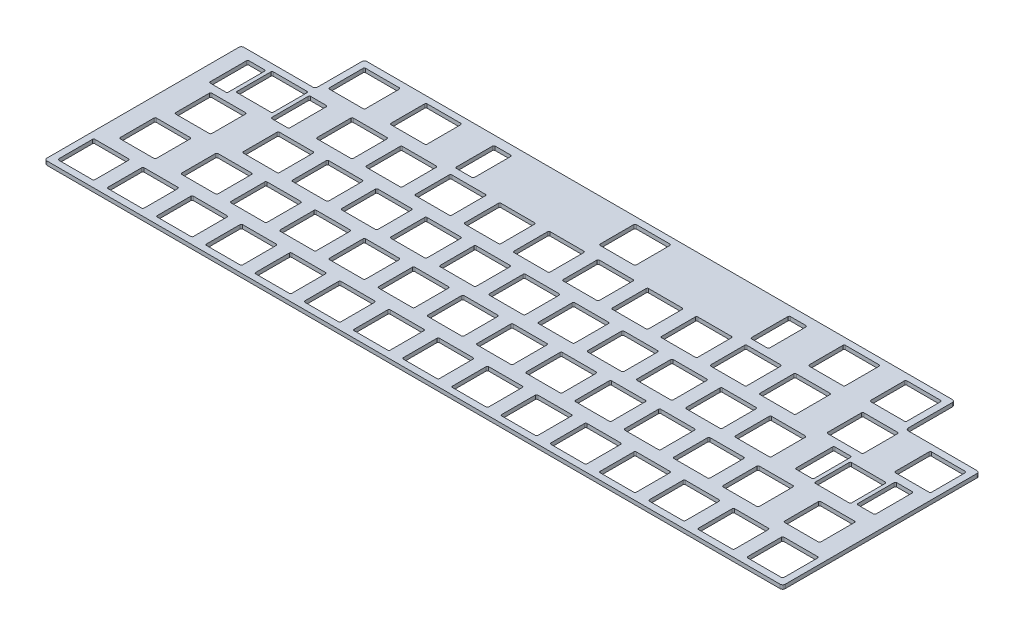
SolidWorks part; units mm, degrees
ref_plane "Front Plane" through (0, 0, 0) normal (0, 0, 1) x (1, 0, 0)
ref_plane "Top Plane" through (0, 0, 0) normal (0, 1, 0) x (1, 0, 0)
ref_plane "Right Plane" through (0, 0, 0) normal (1, 0, 0) x (0, 0, -1)
sketch "Sketch2" plane through (0, 0, 0) normal (0, -1, 0) x (1, 0, 0)
  line L0 (3.025, -2.525) -> (16.025, -2.525)
  line L1 (3.025, -16.525) -> (16.025, -16.525)
  line L2 (2.525, -3.025) -> (2.525, -16.025)
  line L3 (16.525, -3.025) -> (16.525, -16.025)
  line L4 (22.075, -2.525) -> (35.075, -2.525)
  line L5 (22.075, -16.525) -> (35.075, -16.525)
  line L6 (21.575, -3.025) -> (21.575, -16.025)
  line L7 (35.575, -3.025) -> (35.575, -16.025)
  line L8 (41.125, -2.525) -> (54.125, -2.525)
  line L9 (41.125, -16.525) -> (54.125, -16.525)
  line L10 (40.625, -3.025) -> (40.625, -16.025)
  line L11 (54.625, -3.025) -> (54.625, -16.025)
  line L12 (60.175, -2.525) -> (73.175, -2.525)
  line L13 (60.175, -16.525) -> (73.175, -16.525)
  line L14 (59.675, -3.025) -> (59.675, -16.025)
  line L15 (73.675, -3.025) -> (73.675, -16.025)
  line L16 (79.225, -2.525) -> (92.225, -2.525)
  line L17 (79.225, -16.525) -> (92.225, -16.525)
  line L18 (78.725, -3.025) -> (78.725, -16.025)
  line L19 (92.725, -3.025) -> (92.725, -16.025)
  line L20 (98.275, -2.525) -> (111.275, -2.525)
  line L21 (98.275, -16.525) -> (111.275, -16.525)
  line L22 (97.775, -3.025) -> (97.775, -16.025)
  line L23 (111.775, -3.025) -> (111.775, -16.025)
  line L24 (117.325, -2.525) -> (130.325, -2.525)
  line L25 (117.325, -16.525) -> (130.325, -16.525)
  line L26 (116.825, -3.025) -> (116.825, -16.025)
  line L27 (130.825, -3.025) -> (130.825, -16.025)
  line L28 (136.375, -2.525) -> (149.375, -2.525)
  line L29 (136.375, -16.525) -> (149.375, -16.525)
  line L30 (135.875, -3.025) -> (135.875, -16.025)
  line L31 (149.875, -3.025) -> (149.875, -16.025)
  line L32 (155.425, -2.525) -> (168.425, -2.525)
  line L33 (155.425, -16.525) -> (168.425, -16.525)
  line L34 (154.925, -3.025) -> (154.925, -16.025)
  line L35 (168.925, -3.025) -> (168.925, -16.025)
  line L36 (174.475, -2.525) -> (187.475, -2.525)
  line L37 (174.475, -16.525) -> (187.475, -16.525)
  line L38 (173.975, -3.025) -> (173.975, -16.025)
  line L39 (187.975, -3.025) -> (187.975, -16.025)
  line L40 (193.525, -2.525) -> (206.525, -2.525)
  line L41 (193.525, -16.525) -> (206.525, -16.525)
  line L42 (193.025, -3.025) -> (193.025, -16.025)
  line L43 (207.025, -3.025) -> (207.025, -16.025)
  line L44 (212.575, -2.525) -> (225.575, -2.525)
  line L45 (212.575, -16.525) -> (225.575, -16.525)
  line L46 (212.075, -3.025) -> (212.075, -16.025)
  line L47 (226.075, -3.025) -> (226.075, -16.025)
  line L48 (231.625, -2.525) -> (244.625, -2.525)
  line L49 (231.625, -16.525) -> (244.625, -16.525)
  line L50 (231.125, -3.025) -> (231.125, -16.025)
  line L51 (245.125, -3.025) -> (245.125, -16.025)
  line L52 (250.675, -2.525) -> (263.675, -2.525)
  line L53 (250.675, -16.525) -> (263.675, -16.525)
  line L54 (250.175, -3.025) -> (250.175, -16.025)
  line L55 (264.175, -3.025) -> (264.175, -16.025)
  line L56 (269.725, -2.525) -> (282.725, -2.525)
  line L57 (269.725, -16.525) -> (282.725, -16.525)
  line L58 (269.225, -3.025) -> (269.225, -16.025)
  line L59 (283.225, -3.025) -> (283.225, -16.025)
  line L60 (7.7875, -21.575) -> (20.7875, -21.575)
  line L61 (7.7875, -35.575) -> (20.7875, -35.575)
  line L62 (7.2875, -22.075) -> (7.2875, -35.075)
  line L63 (21.2875, -22.075) -> (21.2875, -35.075)
  line L64 (31.6, -21.575) -> (44.6, -21.575)
  line L65 (31.6, -35.575) -> (44.6, -35.575)
  line L66 (31.1, -22.075) -> (31.1, -35.075)
  line L67 (45.1, -22.075) -> (45.1, -35.075)
  line L68 (50.65, -21.575) -> (63.65, -21.575)
  line L69 (50.65, -35.575) -> (63.65, -35.575)
  line L70 (50.15, -22.075) -> (50.15, -35.075)
  line L71 (64.15, -22.075) -> (64.15, -35.075)
  line L72 (69.7, -21.575) -> (82.7, -21.575)
  line L73 (69.7, -35.575) -> (82.7, -35.575)
  line L74 (69.2, -22.075) -> (69.2, -35.075)
  line L75 (83.2, -22.075) -> (83.2, -35.075)
  line L76 (88.75, -21.575) -> (101.75, -21.575)
  line L77 (88.75, -35.575) -> (101.75, -35.575)
  line L78 (88.25, -22.075) -> (88.25, -35.075)
  line L79 (102.25, -22.075) -> (102.25, -35.075)
  line L80 (107.8, -21.575) -> (120.8, -21.575)
  line L81 (107.8, -35.575) -> (120.8, -35.575)
  line L82 (107.3, -22.075) -> (107.3, -35.075)
  line L83 (121.3, -22.075) -> (121.3, -35.075)
  line L84 (126.85, -21.575) -> (139.85, -21.575)
  line L85 (126.85, -35.575) -> (139.85, -35.575)
  line L86 (126.35, -22.075) -> (126.35, -35.075)
  line L87 (140.35, -22.075) -> (140.35, -35.075)
  line L88 (145.9, -21.575) -> (158.9, -21.575)
  line L89 (145.9, -35.575) -> (158.9, -35.575)
  line L90 (145.4, -22.075) -> (145.4, -35.075)
  line L91 (159.4, -22.075) -> (159.4, -35.075)
  line L92 (164.95, -21.575) -> (177.95, -21.575)
  line L93 (164.95, -35.575) -> (177.95, -35.575)
  line L94 (164.45, -22.075) -> (164.45, -35.075)
  line L95 (178.45, -22.075) -> (178.45, -35.075)
  line L96 (184, -21.575) -> (197, -21.575)
  line L97 (184, -35.575) -> (197, -35.575)
  line L98 (183.5, -22.075) -> (183.5, -35.075)
  line L99 (197.5, -22.075) -> (197.5, -35.075)
  line L100 (203.05, -21.575) -> (216.05, -21.575)
  line L101 (203.05, -35.575) -> (216.05, -35.575)
  line L102 (202.55, -22.075) -> (202.55, -35.075)
  line L103 (216.55, -22.075) -> (216.55, -35.075)
  line L104 (222.1, -21.575) -> (235.1, -21.575)
  line L105 (222.1, -35.575) -> (235.1, -35.575)
  line L106 (221.6, -22.075) -> (221.6, -35.075)
  line L107 (235.6, -22.075) -> (235.6, -35.075)
  line L108 (241.15, -21.575) -> (254.15, -21.575)
  line L109 (241.15, -35.575) -> (254.15, -35.575)
  line L110 (240.65, -22.075) -> (240.65, -35.075)
  line L111 (254.65, -22.075) -> (254.65, -35.075)
  line L112 (264.9625, -21.575) -> (277.9625, -21.575)
  line L113 (264.9625, -35.575) -> (277.9625, -35.575)
  line L114 (264.4625, -22.075) -> (264.4625, -35.075)
  line L115 (278.4625, -22.075) -> (278.4625, -35.075)
  line L116 (10.1687, -40.625) -> (23.1687, -40.625)
  line L117 (10.1687, -54.625) -> (23.1687, -54.625)
  line L118 (9.6688, -41.125) -> (9.6688, -54.125)
  line L119 (23.6687, -41.125) -> (23.6687, -54.125)
  line L120 (36.3625, -40.625) -> (49.3625, -40.625)
  line L121 (36.3625, -54.625) -> (49.3625, -54.625)
  line L122 (35.8625, -41.125) -> (35.8625, -54.125)
  line L123 (49.8625, -41.125) -> (49.8625, -54.125)
  line L124 (55.4125, -40.625) -> (68.4125, -40.625)
  line L125 (55.4125, -54.625) -> (68.4125, -54.625)
  line L126 (54.9125, -41.125) -> (54.9125, -54.125)
  line L127 (68.9125, -41.125) -> (68.9125, -54.125)
  line L128 (74.4625, -40.625) -> (87.4625, -40.625)
  line L129 (74.4625, -54.625) -> (87.4625, -54.625)
  line L130 (73.9625, -41.125) -> (73.9625, -54.125)
  line L131 (87.9625, -41.125) -> (87.9625, -54.125)
  line L132 (93.5125, -40.625) -> (106.5125, -40.625)
  line L133 (93.5125, -54.625) -> (106.5125, -54.625)
  line L134 (93.0125, -41.125) -> (93.0125, -54.125)
  line L135 (107.0125, -41.125) -> (107.0125, -54.125)
  line L136 (112.5625, -40.625) -> (125.5625, -40.625)
  line L137 (112.5625, -54.625) -> (125.5625, -54.625)
  line L138 (112.0625, -41.125) -> (112.0625, -54.125)
  line L139 (126.0625, -41.125) -> (126.0625, -54.125)
  line L140 (131.6125, -40.625) -> (144.6125, -40.625)
  line L141 (131.6125, -54.625) -> (144.6125, -54.625)
  line L142 (131.1125, -41.125) -> (131.1125, -54.125)
  line L143 (145.1125, -41.125) -> (145.1125, -54.125)
  line L144 (150.6625, -40.625) -> (163.6625, -40.625)
  line L145 (150.6625, -54.625) -> (163.6625, -54.625)
  line L146 (150.1625, -41.125) -> (150.1625, -54.125)
  line L147 (164.1625, -41.125) -> (164.1625, -54.125)
  line L148 (169.7125, -40.625) -> (182.7125, -40.625)
  line L149 (169.7125, -54.625) -> (182.7125, -54.625)
  line L150 (169.2125, -41.125) -> (169.2125, -54.125)
  line L151 (183.2125, -41.125) -> (183.2125, -54.125)
  line L152 (188.7625, -40.625) -> (201.7625, -40.625)
  line L153 (188.7625, -54.625) -> (201.7625, -54.625)
  line L154 (188.2625, -41.125) -> (188.2625, -54.125)
  line L155 (202.2625, -41.125) -> (202.2625, -54.125)
  line L156 (207.8125, -40.625) -> (220.8125, -40.625)
  line L157 (207.8125, -54.625) -> (220.8125, -54.625)
  line L158 (207.3125, -41.125) -> (207.3125, -54.125)
  line L159 (221.3125, -41.125) -> (221.3125, -54.125)
  line L160 (226.8625, -40.625) -> (239.8625, -40.625)
  line L161 (226.8625, -54.625) -> (239.8625, -54.625)
  line L162 (226.3625, -41.125) -> (226.3625, -54.125)
  line L163 (240.3625, -41.125) -> (240.3625, -54.125)
  line L164 (257.8188, -40.625) -> (270.8188, -40.625)
  line L165 (257.8188, -54.625) -> (270.8188, -54.625)
  line L166 (257.3188, -41.125) -> (257.3188, -54.125)
  line L167 (271.3188, -41.125) -> (271.3188, -54.125)
  line L168 (249.3808, -41.625) -> (255.3807, -41.625)
  line L169 (249.3808, -56.625) -> (255.3807, -56.625)
  line L170 (248.8808, -42.125) -> (248.8808, -56.125)
  line L171 (255.8807, -42.125) -> (255.8807, -56.125)
  line L172 (273.2568, -41.625) -> (279.2568, -41.625)
  line L173 (273.2568, -56.625) -> (279.2568, -56.625)
  line L174 (272.7568, -42.125) -> (272.7568, -56.125)
  line L175 (279.7568, -42.125) -> (279.7568, -56.125)
  line L176 (14.9313, -59.675) -> (27.9312, -59.675)
  line L177 (14.9313, -73.675) -> (27.9312, -73.675)
  line L178 (14.4313, -60.175) -> (14.4313, -73.175)
  line L179 (28.4312, -60.175) -> (28.4312, -73.175)
  line L180 (36.3693, -72.675) -> (30.3693, -72.675)
  line L181 (36.3693, -57.675) -> (30.3693, -57.675)
  line L182 (36.8693, -72.175) -> (36.8693, -58.175)
  line L183 (29.8693, -72.175) -> (29.8693, -58.175)
  line L184 (12.4932, -72.675) -> (6.4932, -72.675)
  line L185 (12.4932, -57.675) -> (6.4932, -57.675)
  line L186 (12.9932, -72.175) -> (12.9932, -58.175)
  line L187 (5.9932, -72.175) -> (5.9932, -58.175)
  line L188 (45.8875, -59.675) -> (58.8875, -59.675)
  line L189 (45.8875, -73.675) -> (58.8875, -73.675)
  line L190 (45.3875, -60.175) -> (45.3875, -73.175)
  line L191 (59.3875, -60.175) -> (59.3875, -73.175)
  line L192 (64.9375, -59.675) -> (77.9375, -59.675)
  line L193 (64.9375, -73.675) -> (77.9375, -73.675)
  line L194 (64.4375, -60.175) -> (64.4375, -73.175)
  line L195 (78.4375, -60.175) -> (78.4375, -73.175)
  line L196 (83.9875, -59.675) -> (96.9875, -59.675)
  line L197 (83.9875, -73.675) -> (96.9875, -73.675)
  line L198 (83.4875, -60.175) -> (83.4875, -73.175)
  line L199 (97.4875, -60.175) -> (97.4875, -73.175)
  line L200 (103.0375, -59.675) -> (116.0375, -59.675)
  line L201 (103.0375, -73.675) -> (116.0375, -73.675)
  line L202 (102.5375, -60.175) -> (102.5375, -73.175)
  line L203 (116.5375, -60.175) -> (116.5375, -73.175)
  line L204 (122.0875, -59.675) -> (135.0875, -59.675)
  line L205 (122.0875, -73.675) -> (135.0875, -73.675)
  line L206 (121.5875, -60.175) -> (121.5875, -73.175)
  line L207 (135.5875, -60.175) -> (135.5875, -73.175)
  line L208 (141.1375, -59.675) -> (154.1375, -59.675)
  line L209 (141.1375, -73.675) -> (154.1375, -73.675)
  line L210 (140.6375, -60.175) -> (140.6375, -73.175)
  line L211 (154.6375, -60.175) -> (154.6375, -73.175)
  line L212 (160.1875, -59.675) -> (173.1875, -59.675)
  line L213 (160.1875, -73.675) -> (173.1875, -73.675)
  line L214 (159.6875, -60.175) -> (159.6875, -73.175)
  line L215 (173.6875, -60.175) -> (173.6875, -73.175)
  line L216 (179.2375, -59.675) -> (192.2375, -59.675)
  line L217 (179.2375, -73.675) -> (192.2375, -73.675)
  line L218 (178.7375, -60.175) -> (178.7375, -73.175)
  line L219 (192.7375, -60.175) -> (192.7375, -73.175)
  line L220 (198.2875, -59.675) -> (211.2875, -59.675)
  line L221 (198.2875, -73.675) -> (211.2875, -73.675)
  line L222 (197.7875, -60.175) -> (197.7875, -73.175)
  line L223 (211.7875, -60.175) -> (211.7875, -73.175)
  line L224 (217.3375, -59.675) -> (230.3375, -59.675)
  line L225 (217.3375, -73.675) -> (230.3375, -73.675)
  line L226 (216.8375, -60.175) -> (216.8375, -73.175)
  line L227 (230.8375, -60.175) -> (230.8375, -73.175)
  line L228 (243.5312, -59.675) -> (256.5312, -59.675)
  line L229 (243.5312, -73.675) -> (256.5312, -73.675)
  line L230 (243.0312, -60.175) -> (243.0312, -73.175)
  line L231 (257.0312, -60.175) -> (257.0312, -73.175)
  line L232 (269.725, -59.675) -> (282.725, -59.675)
  line L233 (269.725, -73.675) -> (282.725, -73.675)
  line L234 (269.225, -60.175) -> (269.225, -73.175)
  line L235 (283.225, -60.175) -> (283.225, -73.175)
  line L236 (31.6, -78.725) -> (44.6, -78.725)
  line L237 (31.6, -92.725) -> (44.6, -92.725)
  line L238 (31.1, -79.225) -> (31.1, -92.225)
  line L239 (45.1, -79.225) -> (45.1, -92.225)
  line L240 (55.4125, -78.725) -> (68.4125, -78.725)
  line L241 (55.4125, -92.725) -> (68.4125, -92.725)
  line L242 (54.9125, -79.225) -> (54.9125, -92.225)
  line L243 (68.9125, -79.225) -> (68.9125, -92.225)
  line L244 (136.375, -78.725) -> (149.375, -78.725)
  line L245 (136.375, -92.725) -> (149.375, -92.725)
  line L246 (135.875, -79.225) -> (135.875, -92.225)
  line L247 (149.875, -79.225) -> (149.875, -92.225)
  line L248 (203.025, -91.725) -> (197.025, -91.725)
  line L249 (203.025, -76.725) -> (197.025, -76.725)
  line L250 (203.525, -91.225) -> (203.525, -77.225)
  line L251 (196.525, -91.225) -> (196.525, -77.225)
  line L252 (88.725, -91.725) -> (82.725, -91.725)
  line L253 (88.725, -76.725) -> (82.725, -76.725)
  line L254 (89.225, -91.225) -> (89.225, -77.225)
  line L255 (82.225, -91.225) -> (82.225, -77.225)
  line L256 (217.3375, -78.725) -> (230.3375, -78.725)
  line L257 (217.3375, -92.725) -> (230.3375, -92.725)
  line L258 (216.8375, -79.225) -> (216.8375, -92.225)
  line L259 (230.8375, -79.225) -> (230.8375, -92.225)
  line L260 (241.15, -78.725) -> (254.15, -78.725)
  line L261 (241.15, -92.725) -> (254.15, -92.725)
  line L262 (240.65, -79.225) -> (240.65, -92.225)
  line L263 (254.65, -79.225) -> (254.65, -92.225)
  line L264 (29.575, -95.25) -> (256.175, -95.25)
  line L265 (1, 0) -> (284.75, 0)
  line L266 (0, -75.2) -> (0, -1)
  line L267 (285.75, -75.2) -> (285.75, -1)
  line L268 (284.75, -76.2) -> (258.175, -76.2)
  line L269 (257.175, -77.2) -> (257.175, -94.25)
  line L270 (1, -76.2) -> (27.575, -76.2)
  line L271 (28.575, -77.2) -> (28.575, -94.25)
  arc A0 (3.025, -2.525) -> (2.525, -3.025) centre (3.025, -3.025) ccw
  arc A1 (16.525, -3.025) -> (16.025, -2.525) centre (16.025, -3.025) ccw
  arc A2 (2.525, -16.025) -> (3.025, -16.525) centre (3.025, -16.025) ccw
  arc A3 (16.025, -16.525) -> (16.525, -16.025) centre (16.025, -16.025) ccw
  arc A4 (22.075, -2.525) -> (21.575, -3.025) centre (22.075, -3.025) ccw
  arc A5 (35.575, -3.025) -> (35.075, -2.525) centre (35.075, -3.025) ccw
  arc A6 (21.575, -16.025) -> (22.075, -16.525) centre (22.075, -16.025) ccw
  arc A7 (35.075, -16.525) -> (35.575, -16.025) centre (35.075, -16.025) ccw
  arc A8 (41.125, -2.525) -> (40.625, -3.025) centre (41.125, -3.025) ccw
  arc A9 (54.625, -3.025) -> (54.125, -2.525) centre (54.125, -3.025) ccw
  arc A10 (40.625, -16.025) -> (41.125, -16.525) centre (41.125, -16.025) ccw
  arc A11 (54.125, -16.525) -> (54.625, -16.025) centre (54.125, -16.025) ccw
  arc A12 (60.175, -2.525) -> (59.675, -3.025) centre (60.175, -3.025) ccw
  arc A13 (73.675, -3.025) -> (73.175, -2.525) centre (73.175, -3.025) ccw
  arc A14 (59.675, -16.025) -> (60.175, -16.525) centre (60.175, -16.025) ccw
  arc A15 (73.175, -16.525) -> (73.675, -16.025) centre (73.175, -16.025) ccw
  arc A16 (79.225, -2.525) -> (78.725, -3.025) centre (79.225, -3.025) ccw
  arc A17 (92.725, -3.025) -> (92.225, -2.525) centre (92.225, -3.025) ccw
  arc A18 (78.725, -16.025) -> (79.225, -16.525) centre (79.225, -16.025) ccw
  arc A19 (92.225, -16.525) -> (92.725, -16.025) centre (92.225, -16.025) ccw
  arc A20 (98.275, -2.525) -> (97.775, -3.025) centre (98.275, -3.025) ccw
  arc A21 (111.775, -3.025) -> (111.275, -2.525) centre (111.275, -3.025) ccw
  arc A22 (97.775, -16.025) -> (98.275, -16.525) centre (98.275, -16.025) ccw
  arc A23 (111.275, -16.525) -> (111.775, -16.025) centre (111.275, -16.025) ccw
  arc A24 (117.325, -2.525) -> (116.825, -3.025) centre (117.325, -3.025) ccw
  arc A25 (130.825, -3.025) -> (130.325, -2.525) centre (130.325, -3.025) ccw
  arc A26 (116.825, -16.025) -> (117.325, -16.525) centre (117.325, -16.025) ccw
  arc A27 (130.325, -16.525) -> (130.825, -16.025) centre (130.325, -16.025) ccw
  arc A28 (136.375, -2.525) -> (135.875, -3.025) centre (136.375, -3.025) ccw
  arc A29 (149.875, -3.025) -> (149.375, -2.525) centre (149.375, -3.025) ccw
  arc A30 (135.875, -16.025) -> (136.375, -16.525) centre (136.375, -16.025) ccw
  arc A31 (149.375, -16.525) -> (149.875, -16.025) centre (149.375, -16.025) ccw
  arc A32 (155.425, -2.525) -> (154.925, -3.025) centre (155.425, -3.025) ccw
  arc A33 (168.925, -3.025) -> (168.425, -2.525) centre (168.425, -3.025) ccw
  arc A34 (154.925, -16.025) -> (155.425, -16.525) centre (155.425, -16.025) ccw
  arc A35 (168.425, -16.525) -> (168.925, -16.025) centre (168.425, -16.025) ccw
  arc A36 (174.475, -2.525) -> (173.975, -3.025) centre (174.475, -3.025) ccw
  arc A37 (187.975, -3.025) -> (187.475, -2.525) centre (187.475, -3.025) ccw
  arc A38 (173.975, -16.025) -> (174.475, -16.525) centre (174.475, -16.025) ccw
  arc A39 (187.475, -16.525) -> (187.975, -16.025) centre (187.475, -16.025) ccw
  arc A40 (193.525, -2.525) -> (193.025, -3.025) centre (193.525, -3.025) ccw
  arc A41 (207.025, -3.025) -> (206.525, -2.525) centre (206.525, -3.025) ccw
  arc A42 (193.025, -16.025) -> (193.525, -16.525) centre (193.525, -16.025) ccw
  arc A43 (206.525, -16.525) -> (207.025, -16.025) centre (206.525, -16.025) ccw
  arc A44 (212.575, -2.525) -> (212.075, -3.025) centre (212.575, -3.025) ccw
  arc A45 (226.075, -3.025) -> (225.575, -2.525) centre (225.575, -3.025) ccw
  arc A46 (212.075, -16.025) -> (212.575, -16.525) centre (212.575, -16.025) ccw
  arc A47 (225.575, -16.525) -> (226.075, -16.025) centre (225.575, -16.025) ccw
  arc A48 (231.625, -2.525) -> (231.125, -3.025) centre (231.625, -3.025) ccw
  arc A49 (245.125, -3.025) -> (244.625, -2.525) centre (244.625, -3.025) ccw
  arc A50 (231.125, -16.025) -> (231.625, -16.525) centre (231.625, -16.025) ccw
  arc A51 (244.625, -16.525) -> (245.125, -16.025) centre (244.625, -16.025) ccw
  arc A52 (250.675, -2.525) -> (250.175, -3.025) centre (250.675, -3.025) ccw
  arc A53 (264.175, -3.025) -> (263.675, -2.525) centre (263.675, -3.025) ccw
  arc A54 (250.175, -16.025) -> (250.675, -16.525) centre (250.675, -16.025) ccw
  arc A55 (263.675, -16.525) -> (264.175, -16.025) centre (263.675, -16.025) ccw
  arc A56 (269.725, -2.525) -> (269.225, -3.025) centre (269.725, -3.025) ccw
  arc A57 (283.225, -3.025) -> (282.725, -2.525) centre (282.725, -3.025) ccw
  arc A58 (269.225, -16.025) -> (269.725, -16.525) centre (269.725, -16.025) ccw
  arc A59 (282.725, -16.525) -> (283.225, -16.025) centre (282.725, -16.025) ccw
  arc A60 (7.7875, -21.575) -> (7.2875, -22.075) centre (7.7875, -22.075) ccw
  arc A61 (21.2875, -22.075) -> (20.7875, -21.575) centre (20.7875, -22.075) ccw
  arc A62 (7.2875, -35.075) -> (7.7875, -35.575) centre (7.7875, -35.075) ccw
  arc A63 (20.7875, -35.575) -> (21.2875, -35.075) centre (20.7875, -35.075) ccw
  arc A64 (31.6, -21.575) -> (31.1, -22.075) centre (31.6, -22.075) ccw
  arc A65 (45.1, -22.075) -> (44.6, -21.575) centre (44.6, -22.075) ccw
  arc A66 (31.1, -35.075) -> (31.6, -35.575) centre (31.6, -35.075) ccw
  arc A67 (44.6, -35.575) -> (45.1, -35.075) centre (44.6, -35.075) ccw
  arc A68 (50.65, -21.575) -> (50.15, -22.075) centre (50.65, -22.075) ccw
  arc A69 (64.15, -22.075) -> (63.65, -21.575) centre (63.65, -22.075) ccw
  arc A70 (50.15, -35.075) -> (50.65, -35.575) centre (50.65, -35.075) ccw
  arc A71 (63.65, -35.575) -> (64.15, -35.075) centre (63.65, -35.075) ccw
  arc A72 (69.7, -21.575) -> (69.2, -22.075) centre (69.7, -22.075) ccw
  arc A73 (83.2, -22.075) -> (82.7, -21.575) centre (82.7, -22.075) ccw
  arc A74 (69.2, -35.075) -> (69.7, -35.575) centre (69.7, -35.075) ccw
  arc A75 (82.7, -35.575) -> (83.2, -35.075) centre (82.7, -35.075) ccw
  arc A76 (88.75, -21.575) -> (88.25, -22.075) centre (88.75, -22.075) ccw
  arc A77 (102.25, -22.075) -> (101.75, -21.575) centre (101.75, -22.075) ccw
  arc A78 (88.25, -35.075) -> (88.75, -35.575) centre (88.75, -35.075) ccw
  arc A79 (101.75, -35.575) -> (102.25, -35.075) centre (101.75, -35.075) ccw
  arc A80 (107.8, -21.575) -> (107.3, -22.075) centre (107.8, -22.075) ccw
  arc A81 (121.3, -22.075) -> (120.8, -21.575) centre (120.8, -22.075) ccw
  arc A82 (107.3, -35.075) -> (107.8, -35.575) centre (107.8, -35.075) ccw
  arc A83 (120.8, -35.575) -> (121.3, -35.075) centre (120.8, -35.075) ccw
  arc A84 (126.85, -21.575) -> (126.35, -22.075) centre (126.85, -22.075) ccw
  arc A85 (140.35, -22.075) -> (139.85, -21.575) centre (139.85, -22.075) ccw
  arc A86 (126.35, -35.075) -> (126.85, -35.575) centre (126.85, -35.075) ccw
  arc A87 (139.85, -35.575) -> (140.35, -35.075) centre (139.85, -35.075) ccw
  arc A88 (145.9, -21.575) -> (145.4, -22.075) centre (145.9, -22.075) ccw
  arc A89 (159.4, -22.075) -> (158.9, -21.575) centre (158.9, -22.075) ccw
  arc A90 (145.4, -35.075) -> (145.9, -35.575) centre (145.9, -35.075) ccw
  arc A91 (158.9, -35.575) -> (159.4, -35.075) centre (158.9, -35.075) ccw
  arc A92 (164.95, -21.575) -> (164.45, -22.075) centre (164.95, -22.075) ccw
  arc A93 (178.45, -22.075) -> (177.95, -21.575) centre (177.95, -22.075) ccw
  arc A94 (164.45, -35.075) -> (164.95, -35.575) centre (164.95, -35.075) ccw
  arc A95 (177.95, -35.575) -> (178.45, -35.075) centre (177.95, -35.075) ccw
  arc A96 (184, -21.575) -> (183.5, -22.075) centre (184, -22.075) ccw
  arc A97 (197.5, -22.075) -> (197, -21.575) centre (197, -22.075) ccw
  arc A98 (183.5, -35.075) -> (184, -35.575) centre (184, -35.075) ccw
  arc A99 (197, -35.575) -> (197.5, -35.075) centre (197, -35.075) ccw
  arc A100 (203.05, -21.575) -> (202.55, -22.075) centre (203.05, -22.075) ccw
  arc A101 (216.55, -22.075) -> (216.05, -21.575) centre (216.05, -22.075) ccw
  arc A102 (202.55, -35.075) -> (203.05, -35.575) centre (203.05, -35.075) ccw
  arc A103 (216.05, -35.575) -> (216.55, -35.075) centre (216.05, -35.075) ccw
  arc A104 (222.1, -21.575) -> (221.6, -22.075) centre (222.1, -22.075) ccw
  arc A105 (235.6, -22.075) -> (235.1, -21.575) centre (235.1, -22.075) ccw
  arc A106 (221.6, -35.075) -> (222.1, -35.575) centre (222.1, -35.075) ccw
  arc A107 (235.1, -35.575) -> (235.6, -35.075) centre (235.1, -35.075) ccw
  arc A108 (241.15, -21.575) -> (240.65, -22.075) centre (241.15, -22.075) ccw
  arc A109 (254.65, -22.075) -> (254.15, -21.575) centre (254.15, -22.075) ccw
  arc A110 (240.65, -35.075) -> (241.15, -35.575) centre (241.15, -35.075) ccw
  arc A111 (254.15, -35.575) -> (254.65, -35.075) centre (254.15, -35.075) ccw
  arc A112 (264.9625, -21.575) -> (264.4625, -22.075) centre (264.9625, -22.075) ccw
  arc A113 (278.4625, -22.075) -> (277.9625, -21.575) centre (277.9625, -22.075) ccw
  arc A114 (264.4625, -35.075) -> (264.9625, -35.575) centre (264.9625, -35.075) ccw
  arc A115 (277.9625, -35.575) -> (278.4625, -35.075) centre (277.9625, -35.075) ccw
  arc A116 (10.1687, -40.625) -> (9.6688, -41.125) centre (10.1687, -41.125) ccw
  arc A117 (23.6687, -41.125) -> (23.1687, -40.625) centre (23.1687, -41.125) ccw
  arc A118 (9.6688, -54.125) -> (10.1687, -54.625) centre (10.1687, -54.125) ccw
  arc A119 (23.1687, -54.625) -> (23.6687, -54.125) centre (23.1687, -54.125) ccw
  arc A120 (36.3625, -40.625) -> (35.8625, -41.125) centre (36.3625, -41.125) ccw
  arc A121 (49.8625, -41.125) -> (49.3625, -40.625) centre (49.3625, -41.125) ccw
  arc A122 (35.8625, -54.125) -> (36.3625, -54.625) centre (36.3625, -54.125) ccw
  arc A123 (49.3625, -54.625) -> (49.8625, -54.125) centre (49.3625, -54.125) ccw
  arc A124 (55.4125, -40.625) -> (54.9125, -41.125) centre (55.4125, -41.125) ccw
  arc A125 (68.9125, -41.125) -> (68.4125, -40.625) centre (68.4125, -41.125) ccw
  arc A126 (54.9125, -54.125) -> (55.4125, -54.625) centre (55.4125, -54.125) ccw
  arc A127 (68.4125, -54.625) -> (68.9125, -54.125) centre (68.4125, -54.125) ccw
  arc A128 (74.4625, -40.625) -> (73.9625, -41.125) centre (74.4625, -41.125) ccw
  arc A129 (87.9625, -41.125) -> (87.4625, -40.625) centre (87.4625, -41.125) ccw
  arc A130 (73.9625, -54.125) -> (74.4625, -54.625) centre (74.4625, -54.125) ccw
  arc A131 (87.4625, -54.625) -> (87.9625, -54.125) centre (87.4625, -54.125) ccw
  arc A132 (93.5125, -40.625) -> (93.0125, -41.125) centre (93.5125, -41.125) ccw
  arc A133 (107.0125, -41.125) -> (106.5125, -40.625) centre (106.5125, -41.125) ccw
  arc A134 (93.0125, -54.125) -> (93.5125, -54.625) centre (93.5125, -54.125) ccw
  arc A135 (106.5125, -54.625) -> (107.0125, -54.125) centre (106.5125, -54.125) ccw
  arc A136 (112.5625, -40.625) -> (112.0625, -41.125) centre (112.5625, -41.125) ccw
  arc A137 (126.0625, -41.125) -> (125.5625, -40.625) centre (125.5625, -41.125) ccw
  arc A138 (112.0625, -54.125) -> (112.5625, -54.625) centre (112.5625, -54.125) ccw
  arc A139 (125.5625, -54.625) -> (126.0625, -54.125) centre (125.5625, -54.125) ccw
  arc A140 (131.6125, -40.625) -> (131.1125, -41.125) centre (131.6125, -41.125) ccw
  arc A141 (145.1125, -41.125) -> (144.6125, -40.625) centre (144.6125, -41.125) ccw
  arc A142 (131.1125, -54.125) -> (131.6125, -54.625) centre (131.6125, -54.125) ccw
  arc A143 (144.6125, -54.625) -> (145.1125, -54.125) centre (144.6125, -54.125) ccw
  arc A144 (150.6625, -40.625) -> (150.1625, -41.125) centre (150.6625, -41.125) ccw
  arc A145 (164.1625, -41.125) -> (163.6625, -40.625) centre (163.6625, -41.125) ccw
  arc A146 (150.1625, -54.125) -> (150.6625, -54.625) centre (150.6625, -54.125) ccw
  arc A147 (163.6625, -54.625) -> (164.1625, -54.125) centre (163.6625, -54.125) ccw
  arc A148 (169.7125, -40.625) -> (169.2125, -41.125) centre (169.7125, -41.125) ccw
  arc A149 (183.2125, -41.125) -> (182.7125, -40.625) centre (182.7125, -41.125) ccw
  arc A150 (169.2125, -54.125) -> (169.7125, -54.625) centre (169.7125, -54.125) ccw
  arc A151 (182.7125, -54.625) -> (183.2125, -54.125) centre (182.7125, -54.125) ccw
  arc A152 (188.7625, -40.625) -> (188.2625, -41.125) centre (188.7625, -41.125) ccw
  arc A153 (202.2625, -41.125) -> (201.7625, -40.625) centre (201.7625, -41.125) ccw
  arc A154 (188.2625, -54.125) -> (188.7625, -54.625) centre (188.7625, -54.125) ccw
  arc A155 (201.7625, -54.625) -> (202.2625, -54.125) centre (201.7625, -54.125) ccw
  arc A156 (207.8125, -40.625) -> (207.3125, -41.125) centre (207.8125, -41.125) ccw
  arc A157 (221.3125, -41.125) -> (220.8125, -40.625) centre (220.8125, -41.125) ccw
  arc A158 (207.3125, -54.125) -> (207.8125, -54.625) centre (207.8125, -54.125) ccw
  arc A159 (220.8125, -54.625) -> (221.3125, -54.125) centre (220.8125, -54.125) ccw
  arc A160 (226.8625, -40.625) -> (226.3625, -41.125) centre (226.8625, -41.125) ccw
  arc A161 (240.3625, -41.125) -> (239.8625, -40.625) centre (239.8625, -41.125) ccw
  arc A162 (226.3625, -54.125) -> (226.8625, -54.625) centre (226.8625, -54.125) ccw
  arc A163 (239.8625, -54.625) -> (240.3625, -54.125) centre (239.8625, -54.125) ccw
  arc A164 (257.8188, -40.625) -> (257.3188, -41.125) centre (257.8188, -41.125) ccw
  arc A165 (271.3188, -41.125) -> (270.8188, -40.625) centre (270.8188, -41.125) ccw
  arc A166 (257.3188, -54.125) -> (257.8188, -54.625) centre (257.8188, -54.125) ccw
  arc A167 (270.8188, -54.625) -> (271.3188, -54.125) centre (270.8188, -54.125) ccw
  arc A168 (249.3808, -41.625) -> (248.8808, -42.125) centre (249.3808, -42.125) ccw
  arc A169 (255.8807, -42.125) -> (255.3807, -41.625) centre (255.3807, -42.125) ccw
  arc A170 (248.8808, -56.125) -> (249.3808, -56.625) centre (249.3808, -56.125) ccw
  arc A171 (255.3807, -56.625) -> (255.8807, -56.125) centre (255.3807, -56.125) ccw
  arc A172 (273.2568, -41.625) -> (272.7568, -42.125) centre (273.2568, -42.125) ccw
  arc A173 (279.7568, -42.125) -> (279.2568, -41.625) centre (279.2568, -42.125) ccw
  arc A174 (272.7568, -56.125) -> (273.2568, -56.625) centre (273.2568, -56.125) ccw
  arc A175 (279.2568, -56.625) -> (279.7568, -56.125) centre (279.2568, -56.125) ccw
  arc A176 (14.9313, -59.675) -> (14.4313, -60.175) centre (14.9313, -60.175) ccw
  arc A177 (28.4312, -60.175) -> (27.9312, -59.675) centre (27.9312, -60.175) ccw
  arc A178 (14.4313, -73.175) -> (14.9313, -73.675) centre (14.9313, -73.175) ccw
  arc A179 (27.9312, -73.675) -> (28.4312, -73.175) centre (27.9312, -73.175) ccw
  arc A180 (36.3693, -72.675) -> (36.8693, -72.175) centre (36.3693, -72.175) ccw
  arc A181 (29.8693, -72.175) -> (30.3693, -72.675) centre (30.3693, -72.175) ccw
  arc A182 (36.8693, -58.175) -> (36.3693, -57.675) centre (36.3693, -58.175) ccw
  arc A183 (30.3693, -57.675) -> (29.8693, -58.175) centre (30.3693, -58.175) ccw
  arc A184 (12.4932, -72.675) -> (12.9932, -72.175) centre (12.4932, -72.175) ccw
  arc A185 (5.9932, -72.175) -> (6.4932, -72.675) centre (6.4932, -72.175) ccw
  arc A186 (12.9932, -58.175) -> (12.4932, -57.675) centre (12.4932, -58.175) ccw
  arc A187 (6.4932, -57.675) -> (5.9932, -58.175) centre (6.4932, -58.175) ccw
  arc A188 (45.8875, -59.675) -> (45.3875, -60.175) centre (45.8875, -60.175) ccw
  arc A189 (59.3875, -60.175) -> (58.8875, -59.675) centre (58.8875, -60.175) ccw
  arc A190 (45.3875, -73.175) -> (45.8875, -73.675) centre (45.8875, -73.175) ccw
  arc A191 (58.8875, -73.675) -> (59.3875, -73.175) centre (58.8875, -73.175) ccw
  arc A192 (64.9375, -59.675) -> (64.4375, -60.175) centre (64.9375, -60.175) ccw
  arc A193 (78.4375, -60.175) -> (77.9375, -59.675) centre (77.9375, -60.175) ccw
  arc A194 (64.4375, -73.175) -> (64.9375, -73.675) centre (64.9375, -73.175) ccw
  arc A195 (77.9375, -73.675) -> (78.4375, -73.175) centre (77.9375, -73.175) ccw
  arc A196 (83.9875, -59.675) -> (83.4875, -60.175) centre (83.9875, -60.175) ccw
  arc A197 (97.4875, -60.175) -> (96.9875, -59.675) centre (96.9875, -60.175) ccw
  arc A198 (83.4875, -73.175) -> (83.9875, -73.675) centre (83.9875, -73.175) ccw
  arc A199 (96.9875, -73.675) -> (97.4875, -73.175) centre (96.9875, -73.175) ccw
  arc A200 (103.0375, -59.675) -> (102.5375, -60.175) centre (103.0375, -60.175) ccw
  arc A201 (116.5375, -60.175) -> (116.0375, -59.675) centre (116.0375, -60.175) ccw
  arc A202 (102.5375, -73.175) -> (103.0375, -73.675) centre (103.0375, -73.175) ccw
  arc A203 (116.0375, -73.675) -> (116.5375, -73.175) centre (116.0375, -73.175) ccw
  arc A204 (122.0875, -59.675) -> (121.5875, -60.175) centre (122.0875, -60.175) ccw
  arc A205 (135.5875, -60.175) -> (135.0875, -59.675) centre (135.0875, -60.175) ccw
  arc A206 (121.5875, -73.175) -> (122.0875, -73.675) centre (122.0875, -73.175) ccw
  arc A207 (135.0875, -73.675) -> (135.5875, -73.175) centre (135.0875, -73.175) ccw
  arc A208 (141.1375, -59.675) -> (140.6375, -60.175) centre (141.1375, -60.175) ccw
  arc A209 (154.6375, -60.175) -> (154.1375, -59.675) centre (154.1375, -60.175) ccw
  arc A210 (140.6375, -73.175) -> (141.1375, -73.675) centre (141.1375, -73.175) ccw
  arc A211 (154.1375, -73.675) -> (154.6375, -73.175) centre (154.1375, -73.175) ccw
  arc A212 (160.1875, -59.675) -> (159.6875, -60.175) centre (160.1875, -60.175) ccw
  arc A213 (173.6875, -60.175) -> (173.1875, -59.675) centre (173.1875, -60.175) ccw
  arc A214 (159.6875, -73.175) -> (160.1875, -73.675) centre (160.1875, -73.175) ccw
  arc A215 (173.1875, -73.675) -> (173.6875, -73.175) centre (173.1875, -73.175) ccw
  arc A216 (179.2375, -59.675) -> (178.7375, -60.175) centre (179.2375, -60.175) ccw
  arc A217 (192.7375, -60.175) -> (192.2375, -59.675) centre (192.2375, -60.175) ccw
  arc A218 (178.7375, -73.175) -> (179.2375, -73.675) centre (179.2375, -73.175) ccw
  arc A219 (192.2375, -73.675) -> (192.7375, -73.175) centre (192.2375, -73.175) ccw
  arc A220 (198.2875, -59.675) -> (197.7875, -60.175) centre (198.2875, -60.175) ccw
  arc A221 (211.7875, -60.175) -> (211.2875, -59.675) centre (211.2875, -60.175) ccw
  arc A222 (197.7875, -73.175) -> (198.2875, -73.675) centre (198.2875, -73.175) ccw
  arc A223 (211.2875, -73.675) -> (211.7875, -73.175) centre (211.2875, -73.175) ccw
  arc A224 (217.3375, -59.675) -> (216.8375, -60.175) centre (217.3375, -60.175) ccw
  arc A225 (230.8375, -60.175) -> (230.3375, -59.675) centre (230.3375, -60.175) ccw
  arc A226 (216.8375, -73.175) -> (217.3375, -73.675) centre (217.3375, -73.175) ccw
  arc A227 (230.3375, -73.675) -> (230.8375, -73.175) centre (230.3375, -73.175) ccw
  arc A228 (243.5312, -59.675) -> (243.0312, -60.175) centre (243.5312, -60.175) ccw
  arc A229 (257.0312, -60.175) -> (256.5312, -59.675) centre (256.5312, -60.175) ccw
  arc A230 (243.0312, -73.175) -> (243.5312, -73.675) centre (243.5312, -73.175) ccw
  arc A231 (256.5312, -73.675) -> (257.0312, -73.175) centre (256.5312, -73.175) ccw
  arc A232 (269.725, -59.675) -> (269.225, -60.175) centre (269.725, -60.175) ccw
  arc A233 (283.225, -60.175) -> (282.725, -59.675) centre (282.725, -60.175) ccw
  arc A234 (269.225, -73.175) -> (269.725, -73.675) centre (269.725, -73.175) ccw
  arc A235 (282.725, -73.675) -> (283.225, -73.175) centre (282.725, -73.175) ccw
  arc A236 (31.6, -78.725) -> (31.1, -79.225) centre (31.6, -79.225) ccw
  arc A237 (45.1, -79.225) -> (44.6, -78.725) centre (44.6, -79.225) ccw
  arc A238 (31.1, -92.225) -> (31.6, -92.725) centre (31.6, -92.225) ccw
  arc A239 (44.6, -92.725) -> (45.1, -92.225) centre (44.6, -92.225) ccw
  arc A240 (55.4125, -78.725) -> (54.9125, -79.225) centre (55.4125, -79.225) ccw
  arc A241 (68.9125, -79.225) -> (68.4125, -78.725) centre (68.4125, -79.225) ccw
  arc A242 (54.9125, -92.225) -> (55.4125, -92.725) centre (55.4125, -92.225) ccw
  arc A243 (68.4125, -92.725) -> (68.9125, -92.225) centre (68.4125, -92.225) ccw
  arc A244 (136.375, -78.725) -> (135.875, -79.225) centre (136.375, -79.225) ccw
  arc A245 (149.875, -79.225) -> (149.375, -78.725) centre (149.375, -79.225) ccw
  arc A246 (135.875, -92.225) -> (136.375, -92.725) centre (136.375, -92.225) ccw
  arc A247 (149.375, -92.725) -> (149.875, -92.225) centre (149.375, -92.225) ccw
  arc A248 (203.025, -91.725) -> (203.525, -91.225) centre (203.025, -91.225) ccw
  arc A249 (196.525, -91.225) -> (197.025, -91.725) centre (197.025, -91.225) ccw
  arc A250 (203.525, -77.225) -> (203.025, -76.725) centre (203.025, -77.225) ccw
  arc A251 (197.025, -76.725) -> (196.525, -77.225) centre (197.025, -77.225) ccw
  arc A252 (88.725, -91.725) -> (89.225, -91.225) centre (88.725, -91.225) ccw
  arc A253 (82.225, -91.225) -> (82.725, -91.725) centre (82.725, -91.225) ccw
  arc A254 (89.225, -77.225) -> (88.725, -76.725) centre (88.725, -77.225) ccw
  arc A255 (82.725, -76.725) -> (82.225, -77.225) centre (82.725, -77.225) ccw
  arc A256 (217.3375, -78.725) -> (216.8375, -79.225) centre (217.3375, -79.225) ccw
  arc A257 (230.8375, -79.225) -> (230.3375, -78.725) centre (230.3375, -79.225) ccw
  arc A258 (216.8375, -92.225) -> (217.3375, -92.725) centre (217.3375, -92.225) ccw
  arc A259 (230.3375, -92.725) -> (230.8375, -92.225) centre (230.3375, -92.225) ccw
  arc A260 (241.15, -78.725) -> (240.65, -79.225) centre (241.15, -79.225) ccw
  arc A261 (254.65, -79.225) -> (254.15, -78.725) centre (254.15, -79.225) ccw
  arc A262 (240.65, -92.225) -> (241.15, -92.725) centre (241.15, -92.225) ccw
  arc A263 (254.15, -92.725) -> (254.65, -92.225) centre (254.15, -92.225) ccw
  arc A264 (258.175, -76.2) -> (257.175, -77.2) centre (258.175, -77.2) ccw
  arc A265 (27.575, -76.2) -> (28.575, -77.2) centre (27.575, -77.2) cw
  arc A266 (1, -76.2) -> (0, -75.2) centre (1, -75.2) cw
  arc A267 (28.575, -94.25) -> (29.575, -95.25) centre (29.575, -94.25) ccw
  arc A268 (257.175, -94.25) -> (256.175, -95.25) centre (256.175, -94.25) cw
  arc A269 (284.75, -76.2) -> (285.75, -75.2) centre (284.75, -75.2) ccw
  arc A270 (284.75, 0) -> (285.75, -1) centre (284.75, -1) cw
  arc A271 (1, 0) -> (0, -1) centre (1, -1) ccw
  dimension "D8" = 1
  dimension "D1" = 2.525
  dimension "D2" = 2.525
  dimension "D3" = 2.525
  dimension "D4" = 2.525
  dimension "D5" = 2.525
  dimension "D6" = 2.525
  dimension "D7" = 2.525
extrude "Boss-Extrude1" add sketch "Sketch2" along normal blind 1.5
